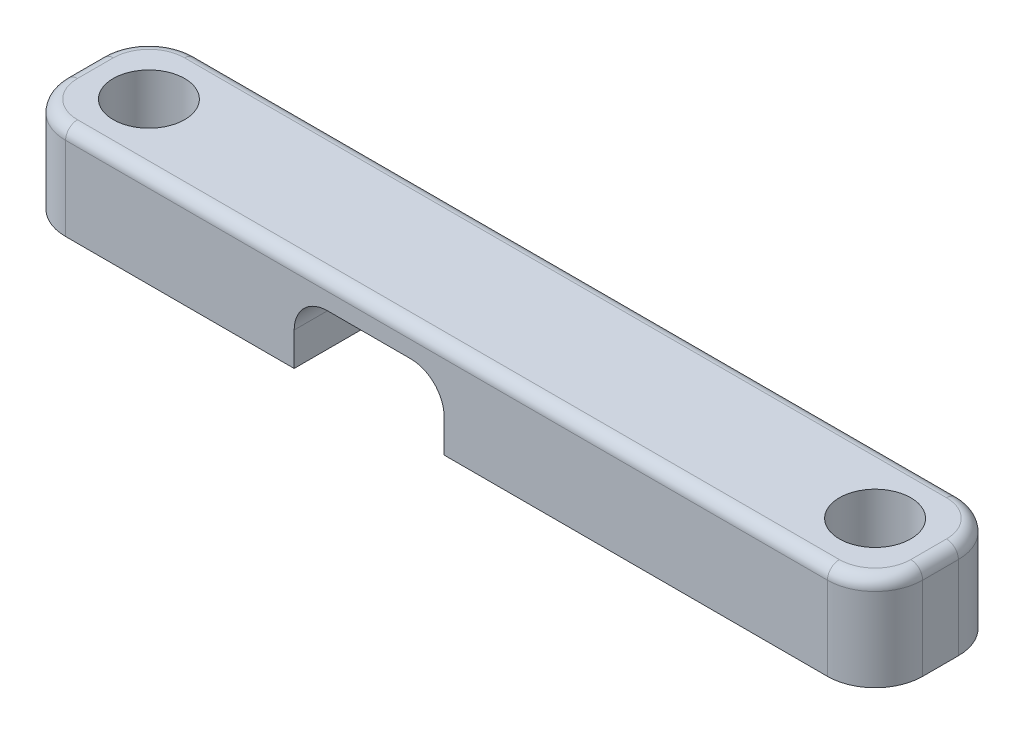
SolidWorks part; units mm, degrees
material "ABS"
ref_plane "Front Plane" through (0, 0, 0) normal (0, 0, 1) x (1, 0, 0)
ref_plane "Top Plane" through (0, 0, 0) normal (0, 1, 0) x (1, 0, 0)
ref_plane "Right Plane" through (0, 0, 0) normal (1, 0, 0) x (0, 0, -1)
sketch "Sketch2" plane through (0, 0, 0) normal (0, 1, 0) x (1, 0, 0)
  line L0 (0, 0) -> (0, 2.75) construction
  line L1 (-18, 2.75) -> (18, 2.75)
  line L2 (-18, 2.75) -> (-18, -2.75)
  line L3 (-18, -2.75) -> (18, -2.75)
  line L4 (18, 2.75) -> (18, -2.75)
  line L5 (-18, 2.75) -> (18, -2.75) construction
  line L6 (-18, -2.75) -> (18, 2.75) construction
  circle A0 centre (-15.25, 0) radius 1.5
  circle A1 centre (15.25, 0) radius 1.5
  point P0 (0, 0)
  dimension "D3" = 3
  dimension "D1" = 5.5
  dimension "D2" = 36
  dimension "D4" = 15.25
extrude "Boss-Extrude1" add sketch "Sketch2" along normal blind 4
sketch "Sketch3" plane through (0, 0, 2.75) normal (0, 0, 1) x (1, 0, 0)
  line L0 (-5, 2.8) -> (-1.5, 2.8)
  line L1 (-18, 4) -> (-18, 0) construction
  line L2 (-18, 0) -> (18, 0) construction
  line L3 (-6.4, 1.4) -> (-6.4, 0)
  line L4 (-6.4, 0) -> (-3.6, 0)
  line L5 (-3.6, 0) -> (-3.6, 1.4)
  line L6 (-2.9, 1.4) -> (-2.9, 0)
  line L7 (-2.9, 0) -> (-0.1, 0)
  line L8 (-0.1, 0) -> (-0.1, 1.4)
  line L9 (-3.6, 0) -> (-2.9, 0)
  circle A2 centre (-5, 1.4) radius 1.4
  circle A3 centre (-1.5, 1.4) radius 1.4
  line M1 (-18, 0) -> (18, 0)
  dimension "D3" = 2.8
  dimension "D4" = 2.8
  dimension "D1" = 13
  dimension "D2" = 16.5
extrude "Cut-Extrude1" cut sketch "Sketch3" against normal up to surface (5.5 mm away) contours A2 | A2 L3 M1 | A2 L4 L5 | A3 L0 A2 L5 L6 M1 | A3 L6 M1 | A3 | A3 L7 L8 up to face at (0, 2, -2.75)
fillet "Fillet1" radius 2 4 edges at (18, 2, -2.75) (18, 2, 2.75) (-18, 2, -2.75) (-18, 2, 2.75)
fillet "Fillet2" radius 0.5 8 edges at (-17.4142, 4, 2.1642) (-18, 4, 0) (-17.4142, 4, -2.1642) (0, 4, -2.75) (17.4142, 4, -2.1642) (18, 4, 0) (17.4142, 4, 2.1642) (0, 4, 2.75)
